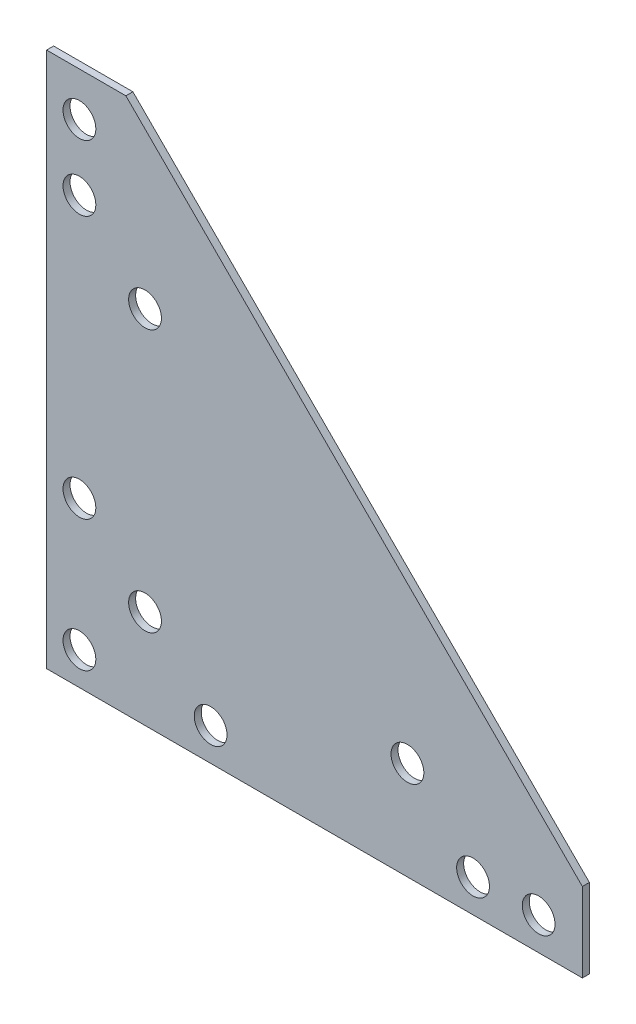
SolidWorks part; units mm, degrees
ref_plane "Front Plane" through (0, 0, 0) normal (0, 0, 1) x (1, 0, 0)
ref_plane "Top Plane" through (0, 0, 0) normal (0, 1, 0) x (1, 0, 0)
ref_plane "Right Plane" through (0, 0, 0) normal (1, 0, 0) x (0, 0, -1)
sketch "Sketch1" plane through (0, 0, 0) normal (0, 0, 1) x (1, 0, 0)
  line L0 (-77.7875, 77.7875) -> (-77.7875, -77.7875) construction
  line L1 (-77.7875, -77.7875) -> (77.7875, -77.7875) construction
  line L2 (77.7875, -77.7875) -> (77.7875, -54.7687) construction
  line L3 (77.7875, -54.7687) -> (-54.7688, 77.7875) construction
  line L4 (-54.7688, 77.7875) -> (-77.7875, 77.7875) construction
  line L5 (0, -77.7875) -> (0, 77.7875) construction
  line L6 (-77.7875, 0) -> (77.7875, 0) construction
  dimension "Length" = 155.575
  dimension "Width" = 155.575
  dimension "D3" = 23.0188
sketch "Sketch2" plane through (0, 0, 0) normal (0, 0, 1) x (1, 0, 0)
  line L0 (-68.2625, 65.0875) -> (-68.2625, 46.0375) construction
  line L1 (-68.2625, 46.0375) -> (-68.2625, -30.1625) construction
  line L2 (-68.2625, -30.1625) -> (-68.2625, -68.2625) construction
  line L3 (-68.2625, -68.2625) -> (-30.1625, -68.2625) construction
  line L4 (-30.1625, -68.2625) -> (46.0375, -68.2625) construction
  line L5 (46.0375, -68.2625) -> (65.0875, -68.2625) construction
  line L6 (-77.7875, -68.2625) -> (-68.2625, -68.2625) construction
  line L7 (-77.7875, 77.7875) -> (-77.7875, -77.7875) construction
  line L8 (-68.2625, -68.2625) -> (-68.2625, -77.7875) construction
  line L9 (-77.7875, -77.7875) -> (77.7875, -77.7875) construction
  line L10 (-49.2125, 26.9875) -> (-49.2125, -49.2125) construction
  line L11 (-49.2125, -49.2125) -> (26.9875, -49.2125) construction
  line L12 (-77.7875, -49.2125) -> (-49.2125, -49.2125) construction
  line L13 (-49.2125, -49.2125) -> (-49.2125, -77.7875) construction
  line L16 (-54.7688, 77.7875) -> (-77.7875, 77.7875) construction
  circle A0 centre (26.9875, -49.2125) radius 4.7625 construction
  dimension "D1" = 9.525
  dimension "D2" = 38.1
  dimension "D3" = 9.525
  dimension "D4" = 9.525
  dimension "D5" = 76.2
  dimension "D6" = 19.05
  dimension "D7" = 76.2
  dimension "D8" = 50.8
sketch "Sketch3" plane through (0, 0, 0) normal (1, 0, 0) x (0, 0, -1)
  line L1 (-1.016, 77.7875) -> (1.016, 77.7875) construction
  line L2 (-1.016, 77.7875) -> (-1.016, -77.7875) construction
  line L3 (-1.016, -77.7875) -> (1.016, -77.7875) construction
  line L4 (1.016, 77.7875) -> (1.016, -77.7875) construction
  dimension "Thickness" = 2.032
sketch "Sketch4" plane through (0, 0, 0) normal (0, 0, 1) x (1, 0, 0)
  line L0 (-54.7688, 77.7875) -> (-77.7875, 77.7875)
  line L1 (-77.7875, 77.7875) -> (-77.7875, -77.7875)
  line L2 (-77.7875, -77.7875) -> (77.7875, -77.7875)
  line L3 (77.7875, -77.7875) -> (77.7875, -54.7687)
  line L4 (77.7875, -54.7687) -> (-54.7688, 77.7875)
extrude "Boss-Extrude1" add sketch "Sketch4" along normal up to vertex (1.016 mm away) and the other way up to vertex (1.016 mm away) up to point (0, 77.7875, 1.016) other way up to point (0, 77.7875, -1.016)
sketch "Sketch5" plane through (0, 0, 0) normal (0, 0, 1) x (1, 0, 0)
  circle A0 centre (-68.2625, 65.0875) radius 4.7625
  circle A1 centre (-68.2625, 46.0375) radius 4.7625
  circle A2 centre (-68.2625, -30.1625) radius 4.7625
  circle A3 centre (-49.2125, 26.9875) radius 4.7625
  circle A4 centre (-49.2125, -49.2125) radius 4.7625
  circle A5 centre (-68.2625, -68.2625) radius 4.7625
  circle A6 centre (-30.1625, -68.2625) radius 4.7625
  circle A7 centre (46.0375, -68.2625) radius 4.7625
  circle A8 centre (26.9875, -49.2125) radius 4.7625
  circle A9 centre (65.0875, -68.2625) radius 4.7625
  circle A10 centre (26.9875, -49.2125) radius 4.7625 construction
extrude "Cut-Extrude1" cut sketch "Sketch5" against normal through all both and the other way through all
